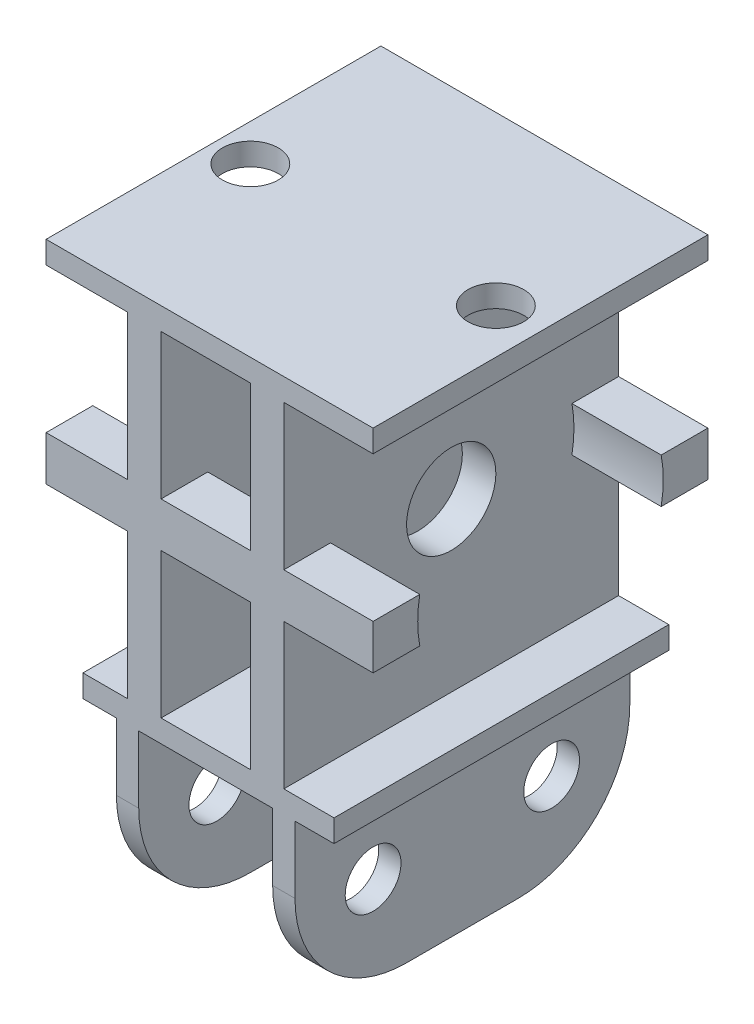
SolidWorks part; units mm, degrees
ref_plane "Alzado" through (0, 0, 0) normal (0, 0, 1) x (1, 0, 0)
ref_plane "Planta" through (0, 0, 0) normal (0, 1, 0) x (1, 0, 0)
ref_plane "Vista lateral" through (0, 0, 0) normal (1, 0, 0) x (0, 0, -1)
sketch "Croquis1" plane through (0, 0, 0) normal (0, 0, 1) x (1, 0, 0)
  line L0 (0, -16) -> (0, 16) construction
  line L1 (-15, -2) -> (-7, -2)
  line L2 (-15, -2) -> (-15, 2)
  line L3 (-15, 2) -> (-7, 2)
  line L4 (15, -2) -> (15, 2)
  line L5 (-15, -2) -> (15, 2) construction
  line L6 (-15, 2) -> (15, -2) construction
  line L7 (-4, 15) -> (4, 15)
  line L8 (-15, 17) -> (15, 17)
  line L9 (-15, 17) -> (-15, 15)
  line L10 (-15, 15) -> (-7, 15)
  line L11 (15, 17) -> (15, 15)
  line L12 (-15, 17) -> (15, 15) construction
  line L13 (-15, 15) -> (15, 17) construction
  line L14 (-15, -17) -> (-8, -17)
  line L15 (-15, -17) -> (-15, -15)
  line L16 (-15, -15) -> (-7, -15)
  line L17 (15, -17) -> (15, -15)
  line L18 (-15, -17) -> (15, -15) construction
  line L19 (-15, -15) -> (15, -17) construction
  line L21 (-7, 15) -> (-7, 2)
  line L23 (-4, 15) -> (-4, 2)
  line L25 (4, 15) -> (4, 2)
  line L27 (7, 15) -> (7, 2)
  line L29 (-7, -2) -> (-7, -15)
  line L31 (-4, -2) -> (-4, -15)
  line L33 (7, -2) -> (7, -15)
  line L35 (4, -2) -> (4, -15)
  line L36 (-4, 2) -> (4, 2)
  line L37 (-4, -2) -> (4, -2)
  line L38 (-4, -15) -> (4, -15)
  line L39 (7, -15) -> (15, -15)
  line L40 (7, -2) -> (15, -2)
  line L41 (7, 2) -> (15, 2)
  line L42 (7, 15) -> (15, 15)
  line L43 (-6, -17) -> (6, -17)
  line L45 (-8, -17) -> (-8, -33)
  line L46 (-8, -33) -> (-6, -33)
  line L47 (-6, -17) -> (-6, -33)
  line L49 (8, -17) -> (8, -33)
  line L50 (8, -33) -> (6, -33)
  line L51 (6, -17) -> (6, -33)
  line L52 (8, -17) -> (15, -17)
  point P0 (0, 0)
  point P9 (0, 0)
  dimension "D1" = 30
  dimension "D2" = 4
  dimension "D3" = 32
  dimension "D4" = 2
  dimension "D5" = 30
  dimension "D6" = 2
  dimension "D7" = 6
  dimension "D8" = 4
  dimension "D9" = 6
  dimension "D10" = 30
  dimension "D11" = 4
  dimension "D12" = 3
  dimension "D13" = 3
  dimension "D16" = 2
  dimension "D17" = 2
  dimension "D18" = 16
  dimension "D19" = 16
extrude "Saliente-Extruir1" add sketch "Croquis1" along normal mid plane 30
sketch "Croquis3" plane through (0, 0, 0) normal (1, 0, 0) x (0, 0, -1)
  circle A0 centre (0, 0) radius 11
  dimension "D1" = 22
extrude "Cortar-Extruir1" cut sketch "Croquis3" against normal mid plane 30
sketch "Croquis4" plane through (8, 0, 0) normal (1, 0, 0) x (0, 0, -1)
  line L0 (0, -17) -> (0, -33) construction
  line L1 (-15, -17) -> (15, -17) construction
  line L2 (-15, -33) -> (15, -33) construction
  line L3 (-15, -25) -> (15, -25) construction
  line L4 (15, -33) -> (15, -17) construction
  circle A0 centre (-8, -25) radius 2.5
  circle A1 centre (8, -25) radius 2.5
  point P11 (0, -25)
  dimension "D1" = 5
  dimension "D2" = 5
  dimension "D3" = 8
  dimension "D4" = 8
extrude "Cortar-Extruir2" cut sketch "Croquis4" against normal blind 30
fillet "Redondeo1" radius 10 4 edges at (-7, -33, 15) (7, -33, 15) (-7, -33, -15) (7, -33, -15)
sketch "Croquis5" plane through (0, 17, 0) normal (0, 1, 0) x (1, 0, 0)
  line L0 (-11, 0) -> (11, 0) construction
  circle A0 centre (-11, 0) radius 2.5
  circle A1 centre (11, 0) radius 2.5
  point P4 (0, 0)
  dimension "D2" = 5
  dimension "D3" = 5
  dimension "D1" = 22
extrude "Cortar-Extruir3" cut sketch "Croquis5" against normal blind 2
sketch "Sketch2" plane through (7, 0, 0) normal (1, 0, 0) x (0, 0, -1)
  circle A0 centre (0, 0) radius 11
  circle A1 centre (0, 0) radius 4
  dimension "D1" = 8
extrude "Boss-Extrude1" add sketch "Sketch2" against normal up to surface (3 mm away) up to face at (4, 7.8333, 0)
sketch "Sketch3" plane through (-7, 0, 0) normal (-1, 0, 0) x (0, 0, 1)
  circle A0 centre (0, 0) radius 11
  circle A1 centre (0, 0) radius 4
extrude "Boss-Extrude2" add sketch "Sketch3" against normal up to surface (3 mm away) up to face at (-4, 7.8333, 0)
sketch "Sketch4" plane through (0, 0, -15) normal (0, 0, -1) x (-1, 0, 0)
  line L0 (-8, -17) -> (-15, -17) construction
  line L1 (-15, -15) -> (-11.5, -15)
  line L2 (-15, -15) -> (-15, -17)
  line L3 (-15, -17) -> (-11.5, -17)
  line L4 (-11.5, -15) -> (-11.5, -17)
  line L5 (7, -15) -> (15, -15) construction
  line L6 (15, -17) -> (11, -17)
  line L7 (15, -17) -> (15, -15)
  line L8 (15, -15) -> (11, -15)
  line L9 (11, -17) -> (11, -15)
extrude "Cut-Extrude1" cut sketch "Sketch4" against normal through all
sketch "Sketch5" plane through (-15, 0, 0) normal (-1, 0, 0) x (0, 0, 1)
  line L1 (-15, 17) -> (15, 17)
  line L2 (-15, 17) -> (-15, -2)
  line L3 (-15, -2) -> (15, -2)
  line L4 (15, 17) -> (15, -2)
extrude "Cut-Extrude2" cut sketch "Sketch5" against normal blind 0.7
